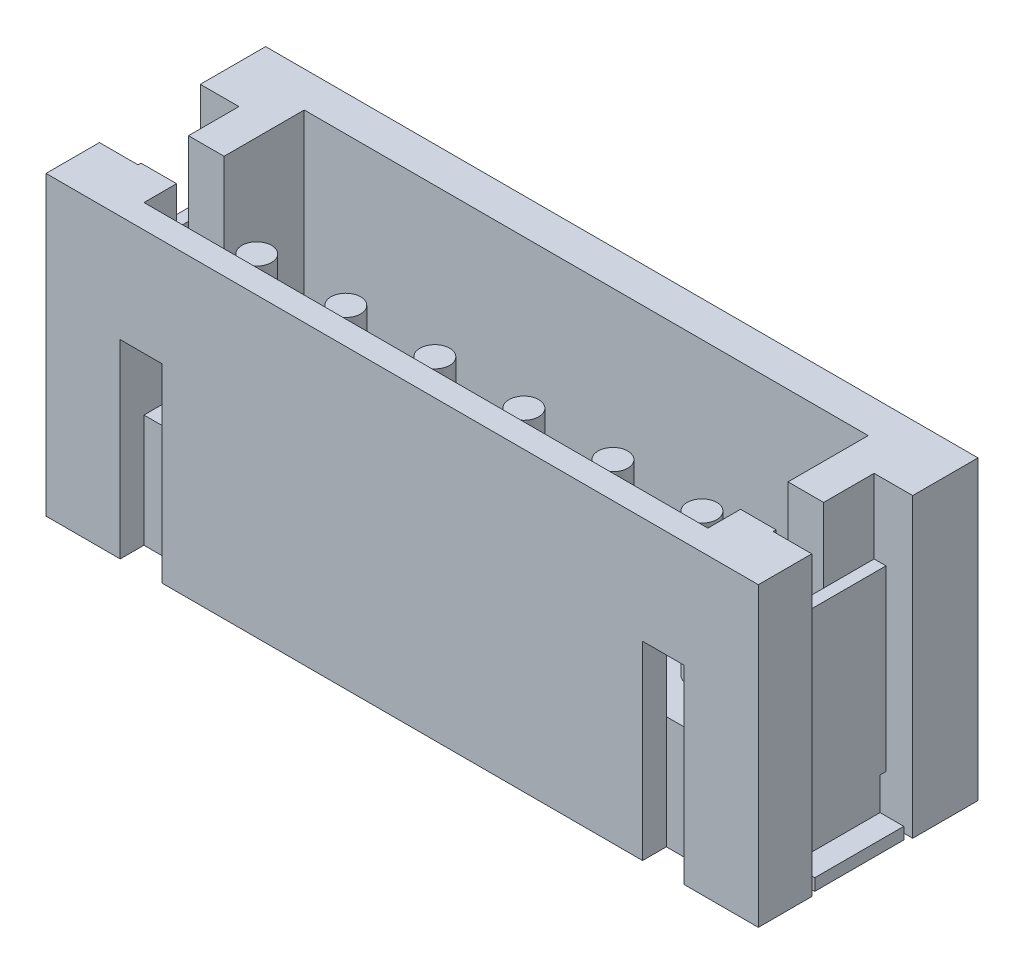
SolidWorks part; units mm, degrees
ref_plane "Front Plane" through (0, 0, 0) normal (0, 0, 1) x (1, 0, 0)
ref_plane "Top Plane" through (0, 0, 0) normal (0, 1, 0) x (1, 0, 0)
ref_plane "Right Plane" through (0, 0, 0) normal (1, 0, 0) x (0, 0, -1)
sketch "Sketch1" plane through (0, 0, 0) normal (0, 0, 1) x (1, 0, 0)
  line L0 (-6, 0) -> (-4.75, 0)
  line L1 (-4.75, 0) -> (-4.75, 5)
  line L2 (-4.75, 5) -> (-6, 5)
  line L3 (-6, 5) -> (-6, 0)
extrude "Boss-Extrude1" add sketch "Sketch1" against normal blind 3.1
sketch "Sketch2" plane through (-4.75, 0, 0) normal (1, 0, 0) x (0, 0, -1)
  line L0 (0, 5) -> (0.4, 5)
  line L1 (0.4, 5) -> (0.4, 1.9)
  line L2 (0.4, 1.9) -> (1.75, 1.9)
  line L3 (1.75, 1.9) -> (2.05, 1.6)
  line L4 (2.05, 1.6) -> (3.1, 1.6)
  line L5 (3.1, 0) -> (0, 0)
  line L6 (0, 0) -> (0, 5)
  spline S0 degree 1 poles (3.1, 0) (3.1, 1.6) knots 0 0 0.32 0.32
extrude "Boss-Extrude2" add sketch "Sketch2" along normal blind 9.5
sketch "Sketch3" plane through (4.75, 0, 0) normal (1, 0, 0) x (0, 0, -1)
  line L0 (3.1, 0) -> (0, 0)
  line L1 (0, 0) -> (0, 5)
  line L2 (0, 5) -> (3.1, 5)
  spline S0 degree 1 poles (3.1, 0) (3.1, 5) knots 0 0 1 1
extrude "Boss-Extrude3" add sketch "Sketch3" along normal blind 1.25
ref_plane "Plane1" through (4.75, 0, 0) normal (1, 0, 0) x (0, 0, -1)
sketch "Sketch4" plane through (4.75, 0, 0) normal (1, 0, 0) x (0, 0, -1)
  line L0 (0.4, 1.9) -> (0.4, 3.2)
  line L1 (0.4, 3.2) -> (0, 3.2)
  line L2 (0, 3.2) -> (0, 0)
  line L3 (0, 0) -> (0.4, 0)
  line L4 (0.4, 0) -> (0.4, 1.9)
extrude "Cut-Extrude1" cut sketch "Sketch4" against normal blind 0.7
ref_plane "Plane2" through (-4.75, 0, 0) normal (-1, 0, 0) x (0, -1, 0)
sketch "Sketch5" plane through (-4.75, 0, 0) normal (-1, 0, 0) x (0, -1, 0)
  line L0 (-1.9, -0.4) -> (0, -0.4)
  line L1 (0, -0.4) -> (0, 0)
  line L2 (0, 0) -> (-3.2, 0)
  line L3 (-3.2, 0) -> (-3.2, -0.4)
  line L4 (-3.2, -0.4) -> (-1.9, -0.4)
extrude "Cut-Extrude2" cut sketch "Sketch5" against normal blind 0.7
sketch "Sketch6" plane through (0, 0, -3.1) normal (0, 0, -1) x (-1, 0, 0)
  spline S0 degree 1 poles (6, 0) (-6, 0) knots 0 0 1 1
  spline S1 degree 1 poles (-6, 0) (-6, 5) knots 0 0 1 1
  spline S2 degree 1 poles (6, 5) (-6, 5) knots 0 0 1 1
  spline S3 degree 1 poles (6, 0) (6, 5) knots 0 0 1 1
extrude "Boss-Extrude4" add sketch "Sketch6" along normal blind 0.6
sketch "Sketch7" plane through (0, 0, 0) normal (0, -1, 0) x (1, 0, 0)
  line L0 (-6, -2.6) -> (-5.55, -2.6)
  line L1 (-5.55, -2.6) -> (-5.55, -0.9)
  line L2 (-5.55, -0.9) -> (-6, -0.9)
  line L3 (-6, -0.9) -> (-6, -2.6)
extrude "Cut-Extrude3" cut sketch "Sketch7" against normal through all
sketch "Sketch8" plane through (-5.55, 0, 0) normal (-1, 0, 0) x (0, 0, 1)
  line L0 (-1.75, 5) -> (-1.75, 3.75)
  line L1 (-1.75, 3.75) -> (-0.95, 3.75)
  line L2 (-0.95, 3.75) -> (-0.95, 5)
  line L3 (-0.95, 5) -> (-1.75, 5)
extrude "Cut-Extrude4" cut sketch "Sketch8" against normal up to next
sketch "Sketch9" plane through (-5.55, 0, 0) normal (-1, 0, 0) x (0, 0, 1)
  line L0 (-2.6, 3.75) -> (-1.75, 3.75)
  line L1 (-1.75, 3.75) -> (-1.75, 5)
  line L2 (-1.75, 5) -> (-2.6, 5)
  line L3 (-2.6, 5) -> (-2.6, 3.75)
extrude "Cut-Extrude5" cut sketch "Sketch9" against normal blind 0.2
sketch "Sketch10" plane through (-5.55, 0, 0) normal (-1, 0, 0) x (0, 0, 1)
  line L0 (-0.95, 3.75) -> (-0.9, 3.75)
  line L1 (-0.9, 3.75) -> (-0.9, 5)
  line L2 (-0.9, 5) -> (-0.95, 5)
  line L3 (-0.95, 5) -> (-0.95, 3.75)
extrude "Cut-Extrude6" cut sketch "Sketch10" against normal blind 0.2
ref_plane "Plane3" through (0, 3.75, 0) normal (0, 1, 0) x (1, 0, 0)
ref_plane "Plane4" through (0, 3.2, 0) normal (0, -1, 0) x (1, 0, 0)
sketch "Sketch12" plane through (0, 3.2, 0) normal (0, -1, 0) x (1, 0, 0)
  line L0 (-4.75, -0.95) -> (-5.35, -0.95)
  line L1 (-5.35, -0.95) -> (-5.35, -1.75)
  line L2 (-5.35, -1.75) -> (-4.75, -1.75)
  line L3 (-4.75, -1.75) -> (-4.75, -0.95)
extrude "Cut-Extrude7" cut sketch "Sketch12" against normal up to surface up to plane "Plane3"
sketch "Sketch13" plane through (0, 0, 0) normal (0, -1, 0) x (1, 0, 0)
  line L0 (6, -0.9) -> (5.55, -0.9)
  line L1 (5.55, -0.9) -> (5.55, -2.6)
  line L2 (5.55, -2.6) -> (6, -2.6)
  line L3 (6, -2.6) -> (6, -0.9)
extrude "Cut-Extrude8" cut sketch "Sketch13" against normal through all
sketch "Sketch14" plane through (5.55, 0, 0) normal (1, 0, 0) x (0, 0, -1)
  line L0 (0.95, 5) -> (0.95, 3.75)
  line L1 (0.95, 3.75) -> (1.75, 3.75)
  line L2 (1.75, 3.75) -> (1.75, 5)
  line L3 (1.75, 5) -> (0.95, 5)
extrude "Cut-Extrude9" cut sketch "Sketch14" against normal through all
sketch "Sketch15" plane through (5.55, 0, 0) normal (1, 0, 0) x (0, 0, -1)
  line L0 (2.6, 3.75) -> (2.6, 5)
  line L1 (2.6, 5) -> (1.75, 5)
  line L2 (1.75, 5) -> (1.75, 3.75)
  line L3 (1.75, 3.75) -> (2.6, 3.75)
extrude "Cut-Extrude10" cut sketch "Sketch15" against normal blind 0.2
ref_plane "Plane5" through (-5.55, 0, 0) normal (-1, 0, 0) x (0, -1, 0)
ref_plane "Plane6" through (-5.35, 0, 0) normal (1, 0, 0) x (0, 0, -1)
sketch "Sketch17" plane through (-5.35, 0, 0) normal (1, 0, 0) x (0, 0, -1)
  line L0 (1, 0) -> (1, 0.75)
  line L1 (1, 0.75) -> (0.9, 0.75)
  line L2 (0.9, 0.75) -> (0.9, 0)
  line L3 (0.9, 0) -> (1, 0)
extrude "Cut-Extrude11" cut sketch "Sketch17" against normal up to surface up to plane "Plane5"
sketch "Sketch18" plane through (-5.55, 0, 0) normal (-1, 0, 0) x (0, 0, 1)
  line L0 (-1, 0.2) -> (-1, 0)
  line L1 (-1, 0) -> (-2.5, 0)
  line L2 (-2.5, 0) -> (-2.5, 0.2)
  line L3 (-2.5, 0.2) -> (-1, 0.2)
extrude "Boss-Extrude5" add sketch "Sketch18" along normal blind 0.4
sketch "Sketch20" plane through (-5.35, 0, 0) normal (1, 0, 0) x (0, 0, -1)
  line L0 (2.6, 0.75) -> (2.5, 0.75)
  line L1 (2.5, 0.75) -> (2.5, 0)
  line L2 (2.5, 0) -> (2.6, 0)
  line L3 (2.6, 0) -> (2.6, 0.75)
extrude "Cut-Extrude12" cut sketch "Sketch20" against normal up to surface up to plane "Plane5"
ref_plane "Plane7" through (5.55, 0, 0) normal (1, 0, 0) x (0, 0, -1)
ref_plane "Plane8" through (5.35, 0, 0) normal (-1, 0, 0) x (0, -1, 0)
sketch "Sketch22" plane through (5.35, 0, 0) normal (-1, 0, 0) x (0, -1, 0)
  line L0 (0, -2.6) -> (0, -2.5)
  line L1 (0, -2.5) -> (-0.75, -2.5)
  line L2 (-0.75, -2.5) -> (-0.75, -2.6)
  line L3 (-0.75, -2.6) -> (0, -2.6)
extrude "Cut-Extrude13" cut sketch "Sketch22" against normal up to surface up to plane "Plane7"
sketch "Sketch23" plane through (5.55, 0, 0) normal (1, 0, 0) x (0, 0, -1)
  line L0 (1, 0) -> (1, 0.2)
  line L1 (1, 0.2) -> (2.5, 0.2)
  line L2 (2.5, 0.2) -> (2.5, 0)
  line L3 (2.5, 0) -> (1, 0)
extrude "Boss-Extrude6" add sketch "Sketch23" along normal blind 0.4
sketch "Sketch25" plane through (5.35, 0, 0) normal (-1, 0, 0) x (0, -1, 0)
  line L0 (0, -0.9) -> (-0.75, -0.9)
  line L1 (-0.75, -0.9) -> (-0.75, -1)
  line L2 (-0.75, -1) -> (0, -1)
  line L3 (0, -1) -> (0, -0.9)
extrude "Cut-Extrude14" cut sketch "Sketch25" against normal up to surface up to plane "Plane7"
sketch "Sketch26" plane through (5.55, 0, 0) normal (1, 0, 0) x (0, 0, -1)
  line L0 (0.95, 3.75) -> (0.95, 5)
  line L1 (0.95, 5) -> (0.9, 5)
  line L2 (0.9, 5) -> (0.9, 3.75)
  line L3 (0.9, 3.75) -> (0.95, 3.75)
extrude "Cut-Extrude15" cut sketch "Sketch26" against normal blind 0.2
sketch "Sketch28" plane through (0, 3.2, 0) normal (0, -1, 0) x (1, 0, 0)
  line L0 (5.35, -1.75) -> (5.35, -0.95)
  line L1 (5.35, -0.95) -> (4.75, -0.95)
  line L2 (4.75, -0.95) -> (4.75, -1.75)
  line L3 (4.75, -1.75) -> (5.35, -1.75)
extrude "Cut-Extrude16" cut sketch "Sketch28" against normal up to surface up to plane "Plane3"
ref_plane "Plane9" through (0, 0, -1.3) normal (0, 0, -1) x (-1, 0, 0)
sketch "Sketch29" plane through (0, 0, -1.3) normal (0, 0, -1) x (-1, 0, 0)
  line L0 (-4, 1.9) -> (-3.75, 1.9)
  line L1 (-3.75, 1.9) -> (-3.75, 4.3)
  line L2 (-3.75, 4.3) -> (-4, 4.3)
  line L3 (-4, 4.3) -> (-4, 1.9)
  line L4 (-3.75, 1.9) -> (-3.75, 4.3) construction
revolve "Revolve1" add sketch "Sketch29" angle 360 about L4
sketch "Sketch30" plane through (0, 0, -1.3) normal (0, 0, -1) x (-1, 0, 0)
  line L0 (-2.5, 1.9) -> (-2.25, 1.9)
  line L1 (-2.25, 1.9) -> (-2.25, 4.3)
  line L2 (-2.25, 4.3) -> (-2.5, 4.3)
  line L3 (-2.5, 4.3) -> (-2.5, 1.9)
  line L4 (-2.25, 1.9) -> (-2.25, 4.3) construction
revolve "Revolve2" add sketch "Sketch30" angle 360 about L4
sketch "Sketch31" plane through (0, 0, -1.3) normal (0, 0, -1) x (-1, 0, 0)
  line L0 (-1, 1.9) -> (-0.75, 1.9)
  line L1 (-0.75, 1.9) -> (-0.75, 4.3)
  line L2 (-0.75, 4.3) -> (-1, 4.3)
  line L3 (-1, 4.3) -> (-1, 1.9)
  line L4 (-0.75, 1.9) -> (-0.75, 4.3) construction
revolve "Revolve3" add sketch "Sketch31" angle 360 about L4
sketch "Sketch32" plane through (0, 0, -1.3) normal (0, 0, -1) x (-1, 0, 0)
  line L0 (0.5, 1.9) -> (0.75, 1.9)
  line L1 (0.75, 1.9) -> (0.75, 4.3)
  line L2 (0.75, 4.3) -> (0.5, 4.3)
  line L3 (0.5, 4.3) -> (0.5, 1.9)
  line L4 (0.75, 1.9) -> (0.75, 4.3) construction
revolve "Revolve4" add sketch "Sketch32" angle 360 about L4
sketch "Sketch33" plane through (0, 0, -1.3) normal (0, 0, -1) x (-1, 0, 0)
  line L0 (2, 1.9) -> (2.25, 1.9)
  line L1 (2.25, 1.9) -> (2.25, 4.3)
  line L2 (2.25, 4.3) -> (2, 4.3)
  line L3 (2, 4.3) -> (2, 1.9)
  line L4 (2.25, 1.9) -> (2.25, 4.3) construction
revolve "Revolve5" add sketch "Sketch33" angle 360 about L4
sketch "Sketch34" plane through (0, 0, -1.3) normal (0, 0, -1) x (-1, 0, 0)
  line L0 (3.5, 1.9) -> (3.75, 1.9)
  line L1 (3.75, 1.9) -> (3.75, 4.3)
  line L2 (3.75, 4.3) -> (3.5, 4.3)
  line L3 (3.5, 4.3) -> (3.5, 1.9)
  line L4 (3.75, 1.9) -> (3.75, 4.3) construction
revolve "Revolve6" add sketch "Sketch34" angle 360 about L4
ref_plane "Plane10" through (0, 0.25, 0) normal (0, -1, 0) x (1, 0, 0)
sketch "Sketch35" plane through (0, 0.25, 0) normal (0, -1, 0) x (1, 0, 0)
  line L0 (4, -3.7) -> (3.75, -3.7)
  line L1 (3.75, -3.7) -> (3.75, -5.2)
  line L2 (3.75, -5.2) -> (4, -5.2)
  line L3 (4, -5.2) -> (4, -3.7)
  line L4 (3.75, -3.7) -> (3.75, -5.2) construction
revolve "Revolve7" add sketch "Sketch35" angle 360 about L4
sketch "Sketch36" plane through (0, 0.25, 0) normal (0, -1, 0) x (1, 0, 0)
  line L0 (2.5, -3.7) -> (2.25, -3.7)
  line L1 (2.25, -3.7) -> (2.25, -5.2)
  line L2 (2.25, -5.2) -> (2.5, -5.2)
  line L3 (2.5, -5.2) -> (2.5, -3.7)
  line L4 (2.25, -3.7) -> (2.25, -5.2) construction
revolve "Revolve8" add sketch "Sketch36" angle 360 about L4
sketch "Sketch37" plane through (0, 0.25, 0) normal (0, -1, 0) x (1, 0, 0)
  line L0 (1, -3.7) -> (0.75, -3.7)
  line L1 (0.75, -3.7) -> (0.75, -5.2)
  line L2 (0.75, -5.2) -> (1, -5.2)
  line L3 (1, -5.2) -> (1, -3.7)
  line L4 (0.75, -3.7) -> (0.75, -5.2) construction
revolve "Revolve9" add sketch "Sketch37" angle 360 about L4
sketch "Sketch38" plane through (0, 0.25, 0) normal (0, -1, 0) x (1, 0, 0)
  line L0 (-0.5, -3.7) -> (-0.75, -3.7)
  line L1 (-0.75, -3.7) -> (-0.75, -5.2)
  line L2 (-0.75, -5.2) -> (-0.5, -5.2)
  line L3 (-0.5, -5.2) -> (-0.5, -3.7)
  line L4 (-0.75, -3.7) -> (-0.75, -5.2) construction
revolve "Revolve10" add sketch "Sketch38" angle 360 about L4
sketch "Sketch39" plane through (0, 0.25, 0) normal (0, -1, 0) x (1, 0, 0)
  line L0 (-2, -3.7) -> (-2.25, -3.7)
  line L1 (-2.25, -3.7) -> (-2.25, -5.2)
  line L2 (-2.25, -5.2) -> (-2, -5.2)
  line L3 (-2, -5.2) -> (-2, -3.7)
  line L4 (-2.25, -3.7) -> (-2.25, -5.2) construction
revolve "Revolve11" add sketch "Sketch39" angle 360 about L4
sketch "Sketch40" plane through (0, 0.25, 0) normal (0, -1, 0) x (1, 0, 0)
  line L0 (-3.5, -3.7) -> (-3.75, -3.7)
  line L1 (-3.75, -3.7) -> (-3.75, -5.2)
  line L2 (-3.75, -5.2) -> (-3.5, -5.2)
  line L3 (-3.5, -5.2) -> (-3.5, -3.7)
  line L4 (-3.75, -3.7) -> (-3.75, -5.2) construction
revolve "Revolve12" add sketch "Sketch40" angle 360 about L4
